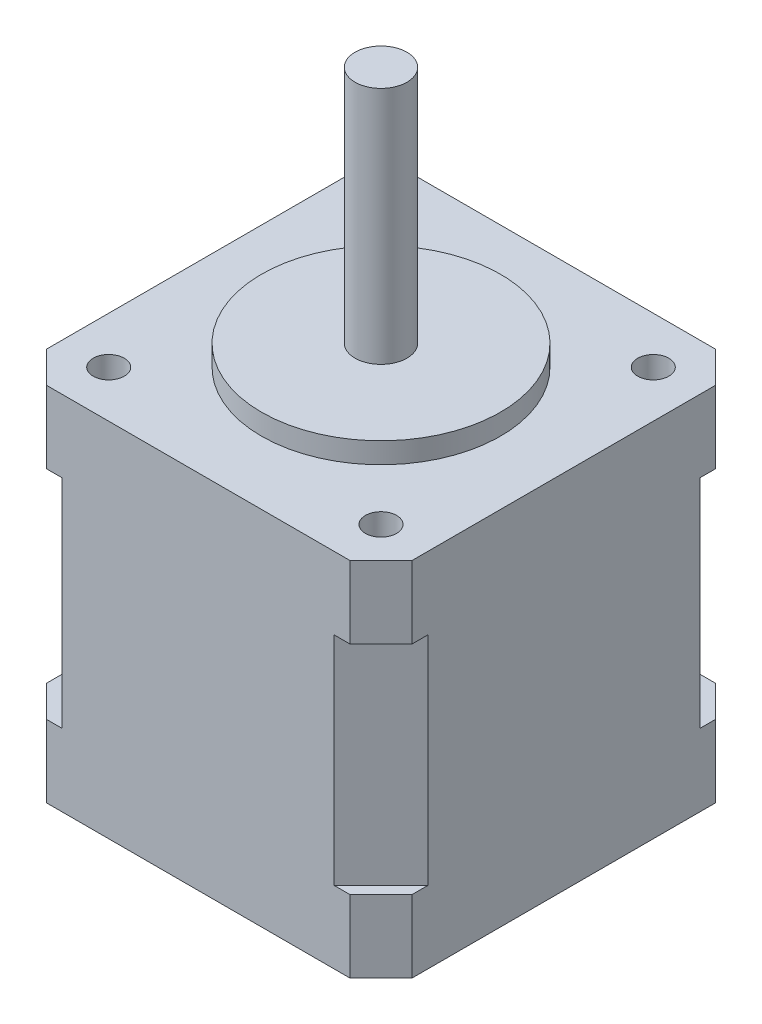
SolidWorks part; units mm, degrees
ref_plane "Front Plane" through (0, 0, 0) normal (0, 0, 1) x (1, 0, 0)
ref_plane "Top Plane" through (0, 0, 0) normal (0, 1, 0) x (1, 0, 0)
ref_plane "Right Plane" through (0, 0, 0) normal (1, 0, 0) x (0, 0, -1)
sketch "Sketch1" plane through (0, 0, 0) normal (0, 1, 0) x (1, 0, 0)
  line L1 (-17.6, 17.6) -> (17.6, 17.6)
  line L2 (-17.6, 17.6) -> (-17.6, -17.6)
  line L3 (-17.6, -17.6) -> (17.6, -17.6)
  line L4 (17.6, 17.6) -> (17.6, -17.6)
  line L5 (-17.6, 17.6) -> (17.6, -17.6) construction
  line L6 (-17.6, -17.6) -> (17.6, 17.6) construction
  point P0 (0, 0)
  dimension "D1" = 35.2
extrude "Boss-Extrude1" add sketch "Sketch1" along normal blind 34.8
sketch "Sketch2" plane through (0, 34.8, 0) normal (0, 1, 0) x (1, 0, 0)
  circle A0 centre (0, 0) radius 11.5
  dimension "D1" = 23
extrude "Boss-Extrude2" add sketch "Sketch2" along normal blind 2 contours A0
sketch "Sketch3" plane through (0, 36.8, 0) normal (0, 1, 0) x (1, 0, 0)
  circle A0 centre (0, 0) radius 2.5
  dimension "D1" = 5
extrude "Boss-Extrude3" add sketch "Sketch3" along normal blind 23
sketch "Sketch4" plane through (0, 34.8, 0) normal (0, 1, 0) x (1, 0, 0)
  line L0 (-17.6, 17.6) -> (-17.6, -17.6) construction
  line L1 (17.6, 17.6) -> (-17.6, 17.6) construction
  circle A0 centre (-13.1, 13.1) radius 1.5
  dimension "D1" = 3
  dimension "D2" = 4.5
  dimension "D3" = 4.5
extrude "Cut-Extrude1" cut sketch "Sketch4" against normal blind 8
mirror "Mirror1" about plane through (0, 0, 0) normal (1, 0, 0) of "Cut-Extrude1"
mirror "Mirror2" about plane through (0, 0, 0) normal (0, 0, 1) of "Mirror1", "Cut-Extrude1"
sketch "Sketch5" plane through (0, 34.8, 0) normal (0, 1, 0) x (1, 0, 0)
  line L0 (-17.6, 17.6) -> (-14.6, 17.6)
  line L1 (17.6, 17.6) -> (-17.6, 17.6) construction
  line L2 (-17.6, 17.6) -> (-17.6, 14.6)
  line L3 (-17.6, 17.6) -> (-17.6, -17.6) construction
  line L4 (-17.6, 14.6) -> (-14.6, 17.6)
  dimension "D1" = 3
  dimension "D2" = 3
extrude "Cut-Extrude2" cut sketch "Sketch5" against normal blind 6.96
mirror "Mirror3" about plane through (0, 0, 0) normal (1, 0, 0) of "Cut-Extrude2"
mirror "Mirror4" about plane through (0, 0, 0) normal (0, 0, 1) of "Mirror3", "Cut-Extrude2"
sketch "Sketch6" plane through (0, 0, 0) normal (0, -1, 0) x (1, 0, 0)
  line L0 (-17.6, 17.6) -> (-14.6, 17.6)
  line L1 (-17.6, 17.6) -> (17.6, 17.6) construction
  line L2 (-17.6, 17.6) -> (-17.6, 14.6)
  line L3 (-17.6, -17.6) -> (-17.6, 17.6) construction
  line L4 (-17.6, 14.6) -> (-14.6, 17.6)
  dimension "D1" = 3
  dimension "D2" = 3
extrude "Cut-Extrude3" cut sketch "Sketch6" against normal blind 6.96
mirror "Mirror5" about plane through (0, 0, 0) normal (1, 0, 0) of "Cut-Extrude3"
mirror "Mirror6" about plane through (0, 0, 0) normal (0, 0, 1) of "Cut-Extrude3", "Mirror5"
sketch "Sketch7" plane through (0, 0, 0) normal (0, -1, 0) x (1, 0, 0)
  circle A0 centre (0, 0) radius 2.5
  dimension "D1" = 5
extrude "Cut-Extrude4" cut sketch "Sketch7" against normal blind 5
sketch "Sketch8" plane through (0, 27.84, 0) normal (0, 1, 0) x (1, 0, 0)
  line L0 (-17.6, 17.6) -> (-13.1, 17.6)
  line L1 (14.6, 17.6) -> (-14.6, 17.6) construction
  line L2 (-17.6, 17.6) -> (-17.6, 13.1)
  line L3 (-17.6, 14.6) -> (-17.6, -14.6) construction
  line L4 (-17.6, 13.1) -> (-13.1, 17.6)
  dimension "D1" = 4.5
  dimension "D2" = 4.5
extrude "Cut-Extrude6" cut sketch "Sketch8" against normal up to surface (20.88 mm away) contours L4 L0 L2 up to face at (-16.6, 6.96, -16.6)
sketch "Sketch9" plane through (0, 27.84, 0) normal (0, 1, 0) x (1, 0, 0)
  line L0 (17.6, 17.6) -> (13.1, 17.6)
  line L1 (14.6, 17.6) -> (-14.6, 17.6) construction
  line L2 (17.6, 17.6) -> (17.6, 13.1)
  line L3 (17.6, -14.6) -> (17.6, 14.6) construction
  line L4 (17.6, 13.1) -> (13.1, 17.6)
  dimension "D1" = 4.5
  dimension "D2" = 4.5
extrude "Cut-Extrude7" cut sketch "Sketch9" against normal up to surface (20.88 mm away) up to face at (16.6, 6.96, -16.6)
sketch "Sketch10" plane through (0, 27.84, 0) normal (0, 1, 0) x (1, 0, 0)
  line L0 (17.6, -17.6) -> (17.6, -13.1)
  line L1 (17.6, -14.6) -> (17.6, 14.6) construction
  line L2 (17.6, -17.6) -> (13.1, -17.6)
  line L3 (-14.6, -17.6) -> (14.6, -17.6) construction
  line L4 (13.1, -17.6) -> (17.6, -13.1)
  dimension "D1" = 4.5
  dimension "D2" = 4.5
extrude "Cut-Extrude8" cut sketch "Sketch10" against normal up to surface (20.88 mm away) up to face at (16.6, 6.96, 16.6)
sketch "Sketch11" plane through (0, 27.84, 0) normal (0, 1, 0) x (1, 0, 0)
  line L0 (-17.6, -17.6) -> (-17.6, -13.1)
  line L1 (-17.6, 14.6) -> (-17.6, -14.6) construction
  line L2 (-17.6, -17.6) -> (-13.1, -17.6)
  line L3 (-14.6, -17.6) -> (14.6, -17.6) construction
  line L4 (-13.1, -17.6) -> (-17.6, -13.1)
  dimension "D1" = 4.5
  dimension "D2" = 4.5
extrude "Cut-Extrude9" cut sketch "Sketch11" against normal up to surface (20.88 mm away) up to face at (-16.6, 6.96, 16.6)
